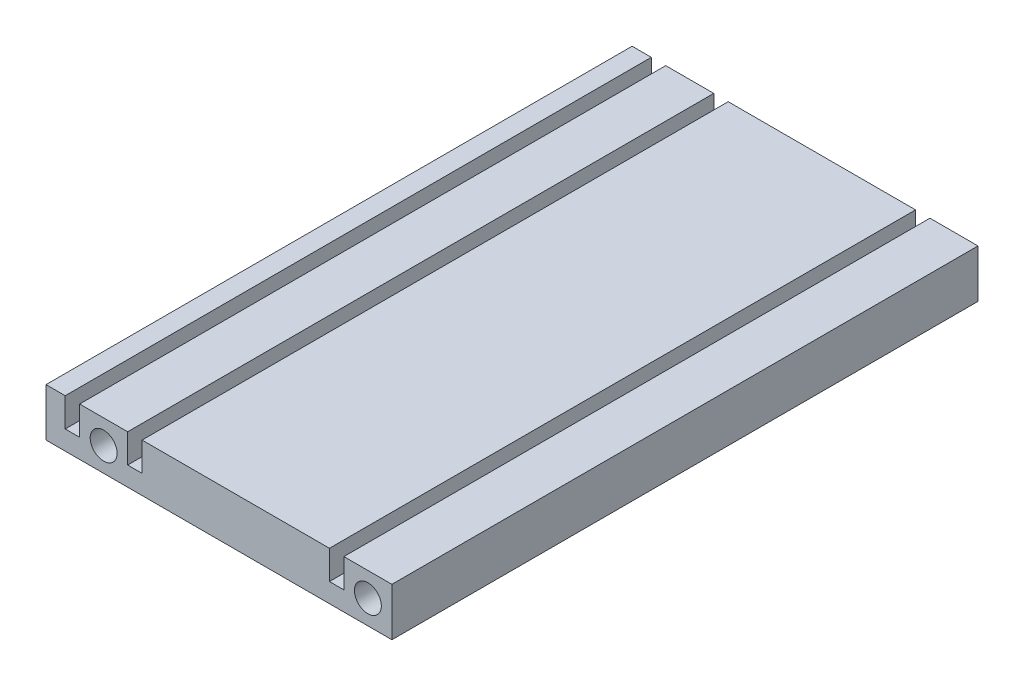
SolidWorks part; units mm, degrees
ref_plane "Plan de face" through (0, 0, 0) normal (0, 0, 1) x (1, 0, 0)
ref_plane "Plan de dessus" through (0, 0, 0) normal (0, 1, 0) x (1, 0, 0)
ref_plane "Plan de droite" through (0, 0, 0) normal (1, 0, 0) x (0, 0, -1)
sketch "Esquisse1" plane through (0, 0, 0) normal (0, 0, 1) x (1, 0, 0)
  line L0 (-35.8911, -3.0896) -> (-35.8911, 6.9104)
  line L1 (-35.8911, 6.9104) -> (-31.8911, 6.9104)
  line L2 (-31.8911, 6.9104) -> (-31.8911, 0.9104)
  line L3 (-31.8911, 0.9104) -> (-28.8911, 0.9104)
  line L4 (-28.8911, 0.9104) -> (-28.8911, 6.9104)
  line L5 (-28.8911, 6.9104) -> (-18.8911, 6.9104)
  line L6 (-18.8911, 6.9104) -> (-18.8911, 0.9104)
  line L7 (-18.8911, 0.9104) -> (-15.8911, 0.9104)
  line L8 (-15.8911, 0.9104) -> (-15.8911, 6.9104)
  line L9 (-15.8911, 6.9104) -> (23.1089, 6.9104)
  line L10 (23.1089, 6.9104) -> (23.1089, 0.9104)
  line L11 (23.1089, 0.9104) -> (26.1089, 0.9104)
  line L12 (26.1089, 0.9104) -> (26.1089, 6.9104)
  line L13 (26.1089, 6.9104) -> (36.1089, 6.9104)
  line L14 (36.1089, 6.9104) -> (36.1089, -3.0896)
  line L15 (36.1089, -3.0896) -> (-35.8911, -3.0896)
  line L16 (-23.8911, 6.9104) -> (-23.8911, -3.0896) construction
  line L17 (31.1089, 6.9104) -> (31.1089, -3.0896) construction
  circle A0 centre (-23.8911, 1.9104) radius 2.8
  circle A1 centre (31.1089, 1.9104) radius 2.8
  point P24 (0, 0)
  point P25 (0, 0)
  dimension "D7" = 5.6
  dimension "D1" = 10
  dimension "D2" = 4
  dimension "D3" = 3
  dimension "D4" = 10
  dimension "D5" = 39
  dimension "D6" = 4
extrude "Boss.-Extru.1" add sketch "Esquisse1" along normal blind 122 contours A1 | A0 | L4 L5 L6 L7 L8 L9 L10 L11 L12 L13 L14 L15 L0 L1 L2 L3
